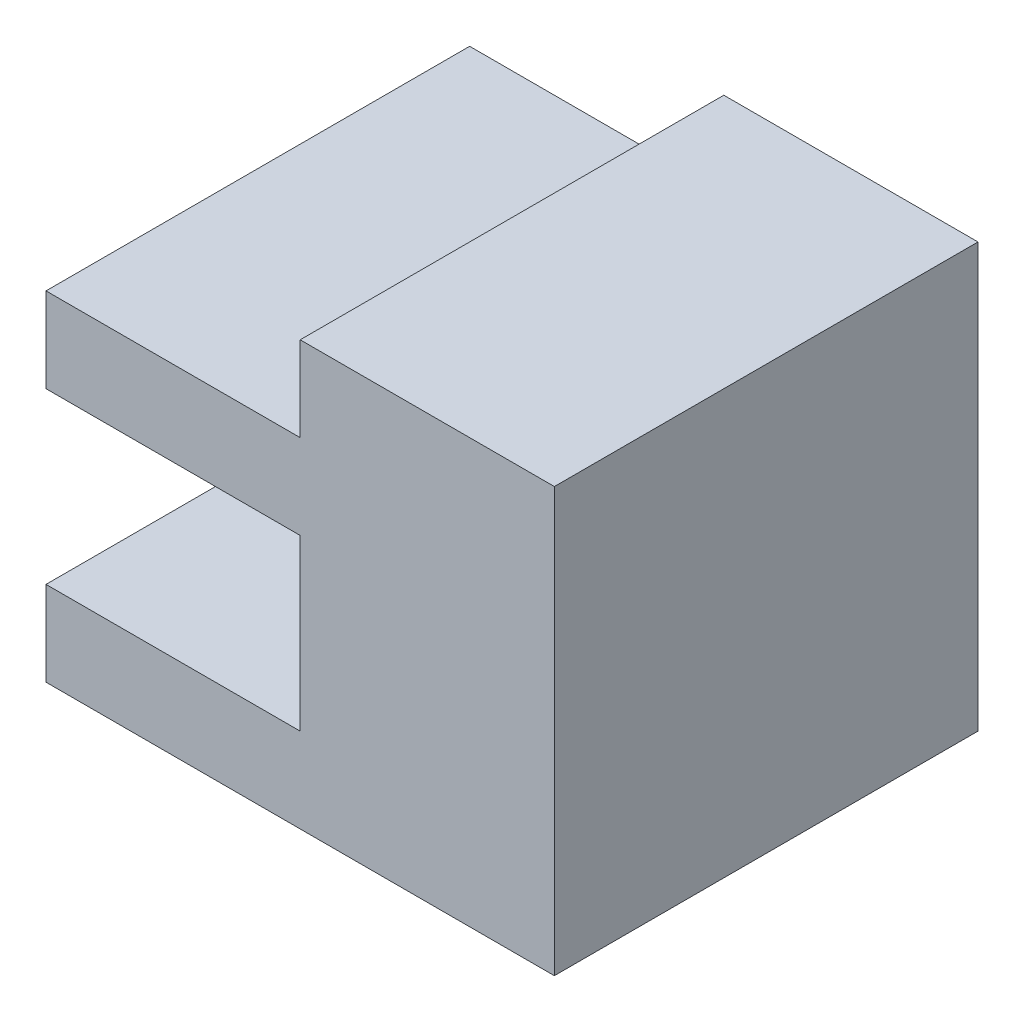
SolidWorks part; units mm, degrees
ref_plane "Front Plane" through (0, 0, 0) normal (0, 0, 1) x (1, 0, 0)
ref_plane "Top Plane" through (0, 0, 0) normal (0, 1, 0) x (1, 0, 0)
ref_plane "Right Plane" through (0, 0, 0) normal (1, 0, 0) x (0, 0, -1)
sketch "Sketch1" plane through (0, 0, 0) normal (0, 0, 1) x (1, 0, 0)
  line L0 (-30, 20) -> (-15, 20)
  line L1 (-15, 20) -> (-15, 25)
  line L2 (-15, 25) -> (0, 25)
  line L3 (0, 25) -> (0, 0)
  line L4 (0, 0) -> (-30, 0)
  line L5 (-30, 0) -> (-30, 5)
  line L6 (-30, 5) -> (-15, 5)
  line L7 (-15, 5) -> (-15, 15)
  line L8 (-15, 15) -> (-30, 15)
  line L9 (-30, 15) -> (-30, 20)
  dimension "D1" = 15
  dimension "D2" = 30
  dimension "D3" = 25
  dimension "D4" = 10
  dimension "D5" = 5
  dimension "D6" = 5
  dimension "D7" = 15
extrude "Boss-Extrude1" add sketch "Sketch1" along normal blind 25
